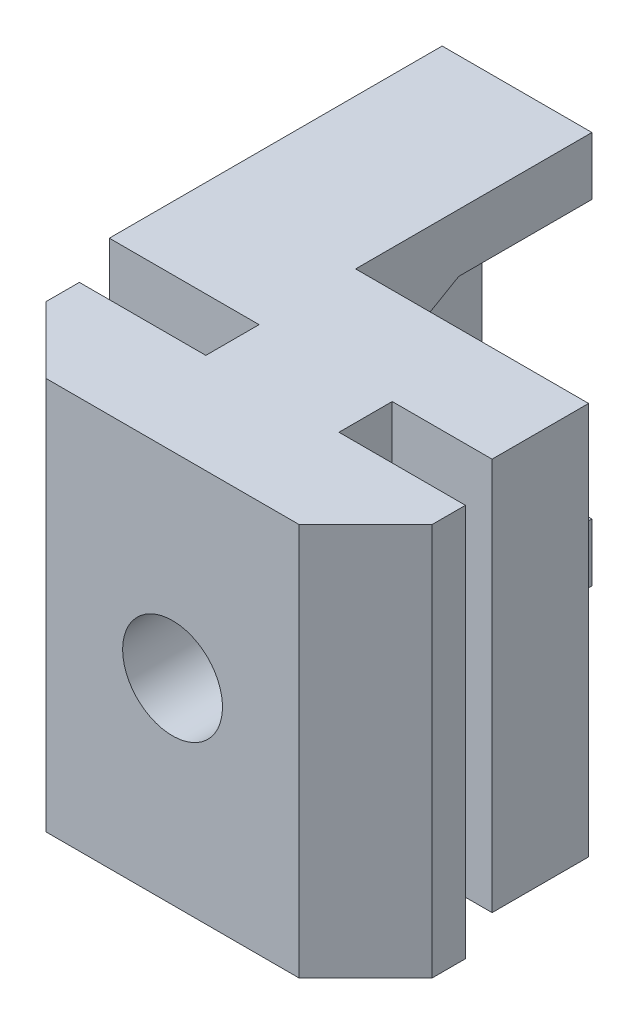
SolidWorks part; units mm, degrees
ref_plane "Front Plane" through (0, 0, 0) normal (0, 0, 1) x (1, 0, 0)
ref_plane "Top Plane" through (0, 0, 0) normal (0, 1, 0) x (1, 0, 0)
ref_plane "Right Plane" through (0, 0, 0) normal (1, 0, 0) x (0, 0, -1)
sketch "Sketch1" plane through (0, 0, 0) normal (0, 1, 0) x (1, 0, 0)
  line L0 (-3.8, 0) -> (-5.8, 2)
  line L1 (-5.8, 2) -> (-5.8, 3)
  line L2 (-5.8, 3) -> (-2, 3)
  line L3 (-2, 3) -> (-2, 4.6)
  line L4 (-2, 4.6) -> (-6.5, 4.6)
  line L5 (-6.5, 4.6) -> (-6.5, 14.6)
  line L6 (-6.5, 14.6) -> (6.5, 14.6)
  line L7 (0, 14.6) -> (0, 0) construction
  line L8 (3.8, 0) -> (-3.8, 0)
  line L9 (6.5, 4.6) -> (6.5, 14.6)
  line L10 (2, 4.6) -> (6.5, 4.6)
  line L11 (2, 3) -> (2, 4.6)
  line L12 (5.8, 3) -> (2, 3)
  line L13 (5.8, 2) -> (5.8, 3)
  line L14 (3.8, 0) -> (5.8, 2)
  dimension "D1" = 3.8
  dimension "D2" = 45
  dimension "D3" = 1
  dimension "D4" = 5.8
  dimension "D5" = 2
  dimension "D6" = 1.6
  dimension "D7" = 10
  dimension "D8" = 6.5
extrude "Boss-Extrude1" add sketch "Sketch1" along normal blind 25
sketch "Sketch2" plane through (0, 25, 0) normal (0, 1, 0) x (1, 0, 0)
  line L6 (6.5, 4.6) -> (5, 4.6)
  line L11 (2, 4.6) -> (6.5, 4.6) construction
  line L12 (5, 4.6) -> (5, 7.5)
  line L13 (5, 7.5) -> (-2, 7.5)
  line L14 (-2, 7.5) -> (-2, 14.6)
  line L15 (6.5, 14.6) -> (-6.5, 14.6) construction
  line L16 (-2, 14.6) -> (6.5, 14.6)
  line L17 (6.5, 14.6) -> (6.5, 4.6)
  line L18 (-3.8, 0) -> (3.8, 0) construction
  line L20 (-6.5, 14.6) -> (-6.5, 4.6) construction
  dimension "D1" = 5
  dimension "D2" = 7.5
  dimension "D3" = 4.5
extrude "Cut-Extrude1" cut sketch "Sketch2" against normal up to next
hole_wizard "M3 Tapped Hole1" positions "Sketch3" profile "Sketch4" tap size "M3" standard "DIN" end condition up to next
sketch "Sketch3" plane through (0, 0, -7.5) normal (0, 0, -1) x (-1, 0, 0)
  line L0 (2, 25) -> (-5, 25) construction
  line L1 (2, 0) -> (-5, 0) construction
  line L2 (-5.8, 25) -> (-5.8, 0) construction
  point P0 (0, 22)
  point P2 (0, 3)
  point P11 (0, 12.5)
  point P18 (-5.8, 12.5)
  dimension "D1" = 3
  dimension "D2" = 3
sketch "Sketch4" plane through (0, 22, -7.5) normal (1, 0, 0) x (0, 1, 0)
  line L0 (0, 0) -> (0, 7.5)
  line L1 (0, 7.5) -> (1.5, 7.5)
  line L2 (1.5, 7.5) -> (1.5, 0)
  line L5 (1.5, 0) -> (0, 0)
  line L11 (0, -6.35) -> (0, 107.95) construction
  dimension "Thread Major Dia." = 3
  dimension "Thru Tap Drill Depth" = 7.5
hole_wizard "M4 Clearance Hole1" positions "Sketch6" profile "Sketch7" hole size "M4" standard "DIN" end condition up to next
sketch "Sketch6" plane through (-6.5, 0, 0) normal (-1, 0, 0) x (0, 0, 1)
  line L0 (-14.6, 25) -> (-14.6, 0) construction
  line L1 (-4.6, 25) -> (-4.6, 0) construction
  point P0 (-10.6, 12.5)
  point P6 (-14.6, 12.5)
  dimension "D1" = 6
sketch "Sketch7" plane through (-6.5, 12.5, -10.6) normal (0, 1, 0) x (0, 0, 1)
  line L0 (0, 0) -> (0, 4.5)
  line L1 (0, 4.5) -> (2.25, 4.5)
  line L2 (2.25, 4.5) -> (2.25, 0)
  line L5 (2.25, 0) -> (0, 0)
  line L11 (0, -6.35) -> (0, 107.95) construction
  dimension "Thru Hole Dia." = 4.5
  dimension "Thru Hole Depth" = 4.5
sketch "Sketch8" plane through (-2, 0, 0) normal (1, 0, 0) x (0, 0, -1)
  line L7 (10.6, 16.6569) -> (14.6, 16.6569)
  line L8 (7, 14.5785) -> (7, 10.4215)
  line L9 (7, 10.4215) -> (10.6, 8.3431)
  line L10 (10.6, 8.3431) -> (14.2, 10.4215) construction
  line L11 (14.2, 10.4215) -> (14.2, 14.5785) construction
  line L12 (14.2, 14.5785) -> (10.6, 16.6569) construction
  line L13 (10.6, 16.6569) -> (7, 14.5785)
  line L14 (14.6, 0) -> (14.6, 25) construction
  line L15 (14.6, 16.6569) -> (14.6, 8.3431)
  line L16 (14.6, 8.3431) -> (10.6, 8.3431)
  circle A1 centre (10.6, 12.5) radius 3.6 construction
  dimension "D1" = 3.6
extrude "Cut-Extrude2" cut sketch "Sketch8" against normal blind 3.3
sketch "Sketch9" plane through (0, 0, -14.6) normal (0, 0, -1) x (-1, 0, 0)
  line L0 (-5.8, 25) -> (-5.8, 0) construction
  line L1 (6.5, 25) -> (-5.8, 25)
  line L2 (6.5, 25) -> (6.5, 18.4)
  line L3 (6.5, 18.4) -> (-5.8, 18.4)
  line L4 (-5.8, 25) -> (-5.8, 18.4)
  line L5 (6.5, 25) -> (6.5, 0) construction
  line L7 (-5.8, 0) -> (6.5, 0)
  line L8 (-5.8, 0) -> (-5.8, 6.6)
  line L9 (-5.8, 6.6) -> (6.5, 6.6)
  line L10 (6.5, 0) -> (6.5, 6.6)
  point P9 (6.5, 12.5)
  dimension "D1" = 5.9
extrude "Cut-Extrude3" cut sketch "Sketch9" against normal through all
